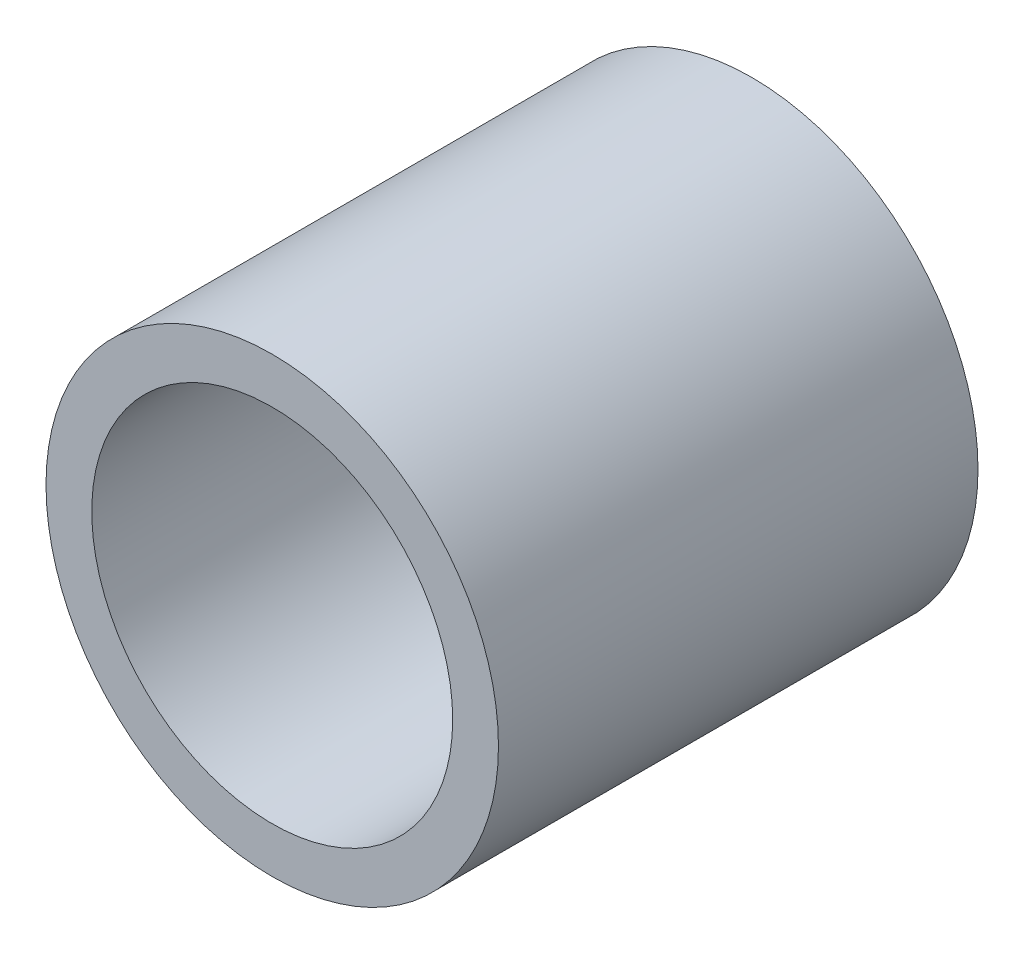
SolidWorks part; units mm, degrees
ref_plane "Alzado" through (0, 0, 0) normal (0, 0, 1) x (1, 0, 0)
ref_plane "Planta" through (0, 0, 0) normal (0, 1, 0) x (1, 0, 0)
ref_plane "Vista lateral" through (0, 0, 0) normal (1, 0, 0) x (0, 0, -1)
sketch "Croquis1" plane through (0, 0, 0) normal (1, 0, 0) x (0, 0, -1)
  line L0 (0, 0) -> (-35.4, 0)
  dimension "D1" = 35.4
other "Miembro estructural1"
ref_plane "Plano1" through (0, 0, 0) normal (0, 0, 1) x (0, -1, 0)
sketch "Sketch1" plane through (0, 0, 0) normal (0, 0, 1) x (0, -1, 0)
  circle A0 centre (0, 0) radius 13.3223
  circle A1 centre (0, 0) radius 16.7005
  circle A2 centre (0, 0) radius 12.7 construction
  point P5 (0, 0)
  dimension "In_dia" = 26.6446
  dimension "Out_dia" = 33.401
  dimension "D1" = 25.4
